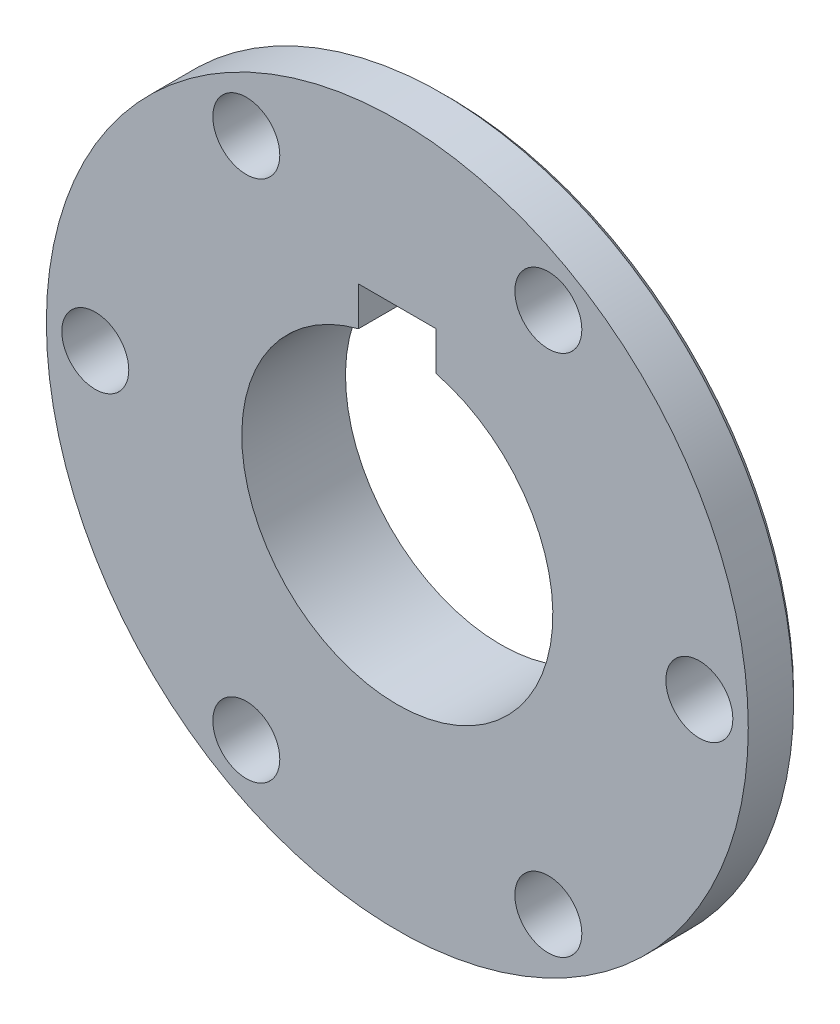
SolidWorks part; units mm, degrees
material "AISI 1045 Steel, cold drawn"
ref_plane "Front Plane" through (0, 0, 0) normal (0, 0, 1) x (1, 0, 0)
ref_plane "Top Plane" through (0, 0, 0) normal (0, 1, 0) x (1, 0, 0)
ref_plane "Right Plane" through (0, 0, 0) normal (1, 0, 0) x (0, 0, -1)
sketch "Sketch1" plane through (0, 0, 0) normal (0, 0, 1) x (1, 0, 0)
  line L0 (-4.7625, 23.2076) -> (-4.7625, 18.4451)
  line L1 (4.7625, 23.2076) -> (4.7625, 18.4451)
  line L2 (0, 0) -> (0, 19.05) construction
  line L7 (4.7625, 23.2076) -> (-4.7625, 23.2076)
  arc A0 (4.7625, 18.4451) -> (-4.7625, 18.4451) centre (0, 0) cw
  circle A1 centre (0, 0) radius 42.9895
  circle A2 centre (0, 0) radius 19.05 construction
  dimension "D1" = 85.979
  dimension "D2" = 4.7625
  dimension "D4" = 19.05
  dimension "D3" = 9.525
sketch "Sketch2" plane through (0, 0, 0) normal (0, 0, 1) x (1, 0, 0)
  circle A0 centre (-18.4976, 32.0387) radius 4.1021
  circle A1 centre (36.9951, 0) radius 4.1021
  circle A2 centre (36.9951, 0) radius 4.1021
  circle A3 centre (18.4976, 32.0387) radius 4.1021
  circle A4 centre (-36.9951, 0) radius 4.1021
  circle A5 centre (-18.4976, -32.0387) radius 4.1021
  circle A6 centre (18.4976, -32.0387) radius 4.1021
extrude "Boss-Extrude1" add sketch "Sketch1" along normal blind 12.7
extrude "Cut-Extrude1" cut sketch "Sketch2" along normal through all contours A1 | A6 | A5 | A4 | A0 | A3
sketch "Sketch3" plane through (0, 0, 0) normal (0, 0, 1) x (1, 0, 0)
  circle A0 centre (0, 0) radius 27.8822
  circle A1 centre (18.4976, 32.0387) radius 7.239 construction
  circle A2 centre (18.4976, 32.0387) radius 10.16 construction
  circle A3 centre (4.7625, 23.2076) radius 4.191 construction
  dimension "D1" = 14.478
  dimension "D2" = 20.32
  dimension "D3" = 8.382
extrude "Cut-Extrude2" cut sketch "Sketch3" along normal blind 6.35 flip side to cut
chamfer "Chamfer1" distance 0.7937 angle 45 2 edges at (27.8822, 0, 0) (42.9895, 0, 6.35)
chamfer "Chamfer2" distance 0.7937 angle 45 1 edges at (27.8822, 0, 6.35)
